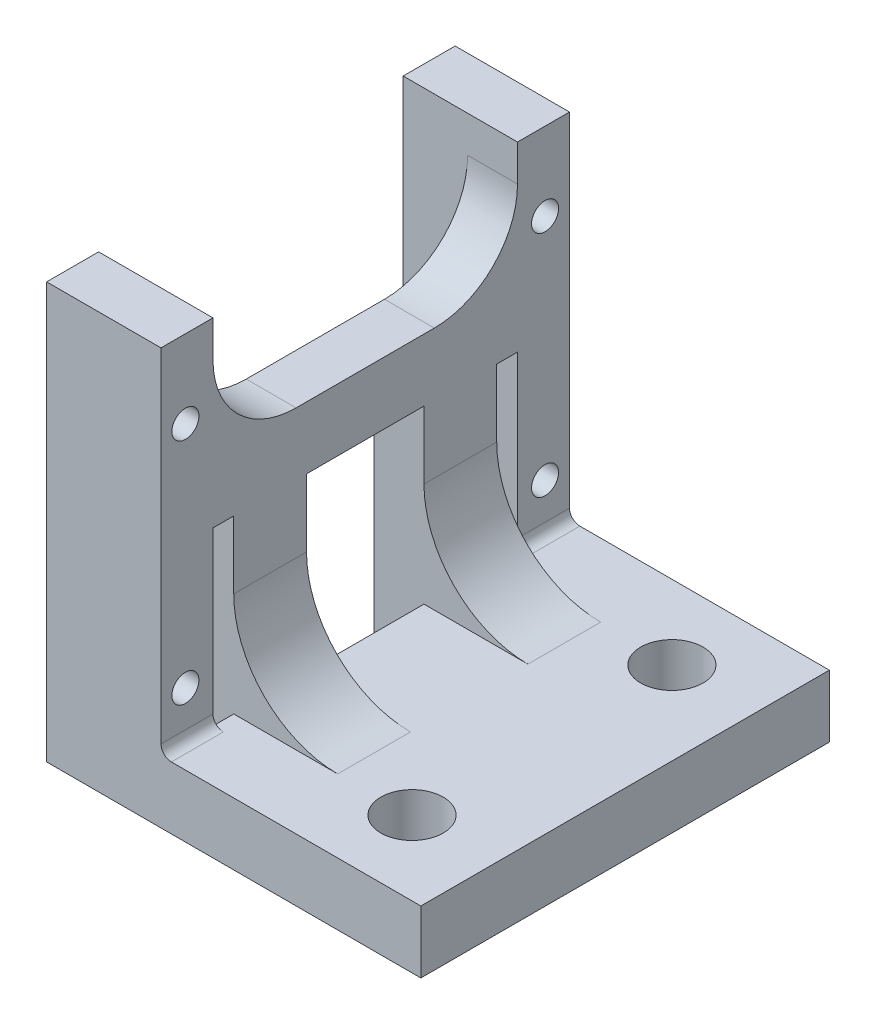
SolidWorks part; units mm, degrees
ref_plane "Front Plane" through (0, 0, 0) normal (0, 0, 1) x (1, 0, 0)
ref_plane "Top Plane" through (0, 0, 0) normal (0, 1, 0) x (1, 0, 0)
ref_plane "Right Plane" through (0, 0, 0) normal (1, 0, 0) x (0, 0, -1)
sketch "Sketch1" plane through (0, 0, 0) normal (1, 0, 0) x (0, 0, -1)
  line L0 (-14.65, 0) -> (14.65, 0) construction
  line L1 (-14.65, 0) -> (-14.65, 40)
  line L2 (14.65, 0) -> (17.3, 0) construction
  line L3 (17.3, 0) -> (17.3, 10.5) construction
  line L4 (-14.65, 0) -> (-17.3, 0) construction
  line L5 (-17.3, 0) -> (-17.3, 10.5) construction
  line L6 (-17.3, 10.5) -> (-17.3, 32.5) construction
  line L7 (17.3, 10.5) -> (17.3, 32.5) construction
  line L8 (14.65, 0) -> (14.65, 40)
  line L9 (14.65, 40) -> (19.65, 40)
  line L10 (-14.65, 40) -> (-19.65, 40)
  line L11 (-19.65, 40) -> (-19.65, 0)
  line L12 (-19.65, 0) -> (-14.65, 0)
  line L13 (19.65, 40) -> (19.65, 0)
  line L14 (19.65, 0) -> (14.65, 0)
  circle A0 centre (-17.3, 32.5) radius 1.3
  circle A1 centre (-17.3, 10.5) radius 1.3
  circle A2 centre (17.3, 10.5) radius 1.3
  circle A3 centre (17.3, 32.5) radius 1.3
  dimension "D4" = 22
  dimension "D7" = 2.6
  dimension "D1" = 29.3
  dimension "D2" = 34.6
  dimension "D3" = 10.5
  dimension "D5" = 5
  dimension "D6" = 40
extrude "Boss-Extrude1" add sketch "Sketch1" along normal blind 11
sketch "Sketch2" plane through (11, 0, 0) normal (1, 0, 0) x (0, 0, -1)
  line L0 (19.65, 0) -> (19.65, 40) construction
  line L1 (-19.65, 0) -> (19.65, 0)
  line L2 (-19.65, 0) -> (-19.65, 6)
  line L3 (-19.65, 6) -> (19.65, 6)
  line L4 (19.65, 0) -> (19.65, 6)
  dimension "D1" = 6
extrude "Boss-Extrude2" add sketch "Sketch2" along normal blind 25
sketch "Sketch3" plane through (11, 0, 0) normal (1, 0, 0) x (0, 0, -1)
  line L0 (-14.65, 6) -> (-14.65, 40) construction
  line L1 (-14.65, 22.5) -> (-12.65, 22.5)
  line L2 (-14.65, 22.5) -> (-14.65, 28.5)
  line L3 (-14.65, 28.5) -> (14.65, 28.5)
  line L4 (14.65, 22.5) -> (14.65, 28.5)
  line L5 (14.65, 40) -> (14.65, 6) construction
  line L7 (12.65, 22.5) -> (14.65, 22.5)
  line L8 (-12.65, 22.5) -> (-12.65, 0)
  line L9 (-12.65, 0) -> (-5.65, 0)
  line L10 (-5.65, 22.5) -> (-5.65, 0)
  line L11 (-5.65, 22.5) -> (5.65, 22.5)
  line L12 (-19.65, 0) -> (19.65, 0) construction
  line L13 (5.65, 22.5) -> (5.65, 0)
  line L14 (5.65, 0) -> (12.65, 0)
  line L15 (12.65, 22.5) -> (12.65, 0)
  circle A0 centre (-17.3, 32.5) radius 1.3 construction
  dimension "D2" = 4
  dimension "D1" = 6
  dimension "D3" = 2
  dimension "D4" = 7
  dimension "D5" = 2
  dimension "D6" = 11.3
extrude "Boss-Extrude3" add sketch "Sketch3" against normal blind 4.8
fillet "Fillet1" radius 1 2 edges at (11, 6, -17.15) (11, 6, 17.15)
sketch "Sketch4" plane through (0, 6, 0) normal (0, 1, 0) x (1, 0, 0)
  line L0 (28, 19.65) -> (28, 12.5) construction
  line L3 (36, 19.65) -> (12, 19.65) construction
  line L4 (36, -19.65) -> (12, -19.65) construction
  line L5 (28, 12.5) -> (28, -12.5) construction
  line L6 (28, -12.5) -> (28, -19.65) construction
  line L7 (36, 19.65) -> (36, -19.65) construction
  circle A0 centre (28, 12.5) radius 3
  circle A1 centre (28, -12.5) radius 3
  dimension "D1" = 25
  dimension "D3" = 6
  dimension "D2" = 8
extrude "Cut-Extrude1" cut sketch "Sketch4" against normal blind 34
fillet "Fillet2" radius 10 2 edges at (11, 6, -9.15) (11, 6, 9.15)
fillet "Fillet3" radius 8 2 edges at (8.6, 28.5, -14.65) (8.6, 28.5, 14.65)
